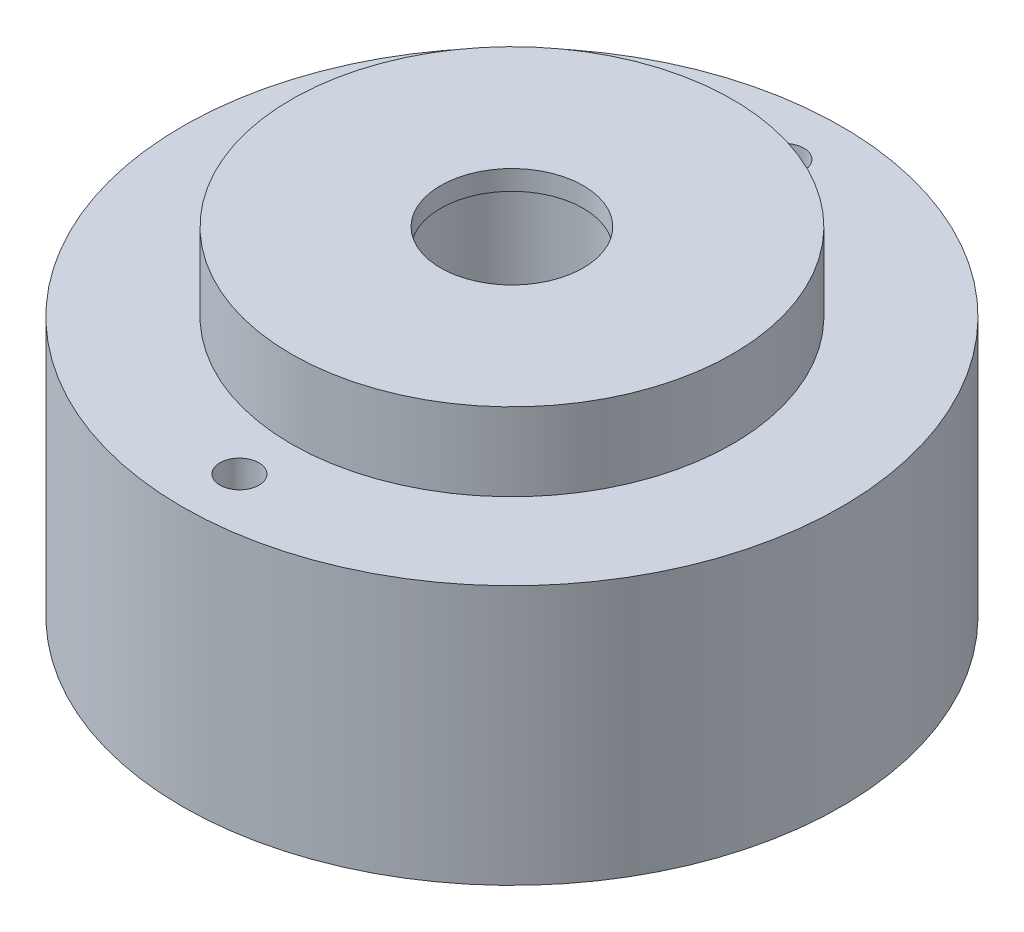
SolidWorks part; units mm, degrees
material "6061-T6 (SS)"
ref_plane "Front Plane" through (0, 0, 0) normal (0, 0, 1) x (1, 0, 0)
ref_plane "Top Plane" through (0, 0, 0) normal (0, 1, 0) x (1, 0, 0)
ref_plane "Right Plane" through (0, 0, 0) normal (1, 0, 0) x (0, 0, -1)
sketch "Sketch1" plane through (0, 0, 0) normal (0, 1, 0) x (1, 0, 0)
  circle A0 centre (0, 0) radius 12.7
  dimension "D1" = 25.4
extrude "Boss-Extrude1" add sketch "Sketch1" along normal blind 10
sketch "Sketch2" plane through (0, 10, 0) normal (0, 1, 0) x (1, 0, 0)
  circle A0 centre (0, 0) radius 8.5
  dimension "D1" = 17
extrude "Boss-Extrude2" add sketch "Sketch2" along normal blind 3
hole_wizard "Ø5.5 (5.5) Diameter Hole1" positions "Sketch3" profile "Sketch4" hole size "Ø5.5" standard "ANSI Metric" end condition through all
sketch "Sketch3" plane through (0, 0, 0) normal (0, -1, 0) x (-1, 0, 0)
  point P0 (0, 0)
sketch "Sketch4" plane through (0, 0, 0) normal (1, 0, 0) x (0, 0, -1)
  line L0 (0, 0) -> (0, 13)
  line L1 (0, 13) -> (2.75, 13)
  line L2 (2.75, 13) -> (2.75, 0)
  line L5 (2.75, 0) -> (0, 0)
  line L11 (0, -6.35) -> (0, 107.95) construction
  dimension "Thru Hole Dia." = 5.5
  dimension "Thru Hole Depth" = 13
hole_wizard "Ø6.3 (6.3) Diameter Hole1" positions "Sketch5" profile "Sketch6" hole size "Ø6.3" standard "ANSI Metric"
sketch "Sketch5" plane through (0, 0, 0) normal (0, -1, 0) x (-1, 0, 0)
  point P0 (0, 0)
sketch "Sketch6" plane through (0, 0, 0) normal (1, 0, 0) x (0, 0, -1)
  line L0 (0, 0) -> (0, 13.8927)
  line L1 (0, 13.8927) -> (3.15, 12)
  line L2 (3.15, 12) -> (3.15, 0)
  line L5 (3.15, 0) -> (0, 0)
  line L10 (0, 13.8927) -> (-3.15, 12) construction
  line L11 (0, -6.35) -> (0, 107.95) construction
  dimension "Hole Dia." = 6.3
  dimension "Hole Depth" = 12
  dimension "Drill Angle" = 118
hole_wizard "Ø1.5mm Dowel Hole1" positions "Sketch7" profile "Sketch8" hole size "Ø1.5" standard "ANSI Metric"
sketch "Sketch7" plane through (0, 10, 0) normal (0, 1, 0) x (1, 0, 0)
  point P0 (0, 10.5)
  point P3 (0, -10.5)
  dimension "D1" = 10.5
  dimension "D2" = 10.5
sketch "Sketch8" plane through (0, 10, -10.5) normal (1, 0, 0) x (0, 0, 1)
  line L0 (0, 0) -> (0, 3.4506)
  line L1 (0, 3.4506) -> (0.75, 3)
  line L2 (0.75, 3) -> (0.75, 0)
  line L5 (0.75, 0) -> (0, 0)
  line L10 (0, 3.4506) -> (-0.75, 3) construction
  line L11 (0, -6.35) -> (0, 107.95) construction
  dimension "Hole Dia." = 1.5
  dimension "Hole Depth" = 3
  dimension "Drill Angle" = 118
